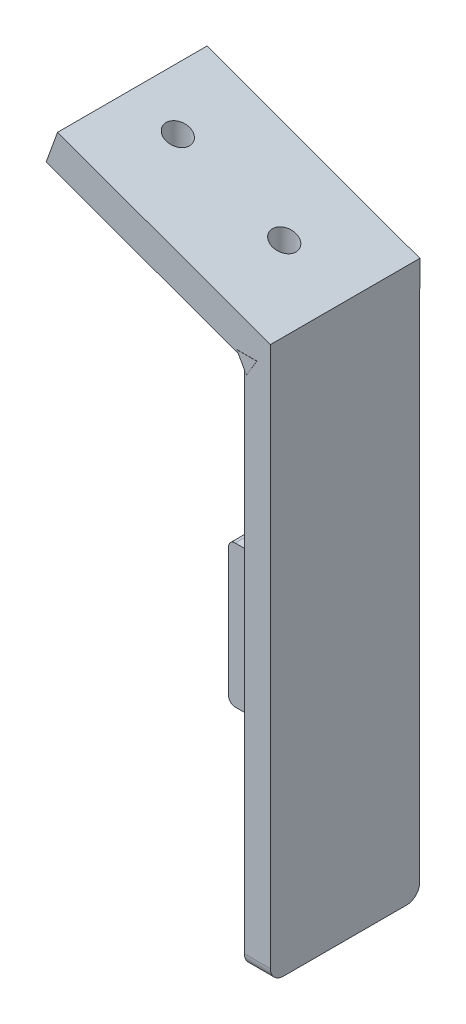
SolidWorks part; units mm, degrees
ref_plane "Plan de face" through (0, 0, 0) normal (0, 0, 1) x (1, 0, 0)
ref_plane "Plan de dessus" through (0, 0, 0) normal (0, 1, 0) x (1, 0, 0)
ref_plane "Plan de droite" through (0, 0, 0) normal (1, 0, 0) x (0, 0, -1)
sketch "Esquisse1" plane through (0, 0, 0) normal (0, 0, 1) x (1, 0, 0)
  line L0 (0, 26.549) -> (0, -58.451)
  line L1 (0, -58.451) -> (-4, -58.451)
  line L2 (-4, -58.451) -> (-4, 26.549)
  line L8 (-4, 26.549) -> (0, 26.549)
extrude "Boss.-Extru.1" add sketch "Esquisse1" along normal blind 22.93
sketch "Esquisse2" plane through (0, 0, 22.93) normal (0, 0, 1) x (1, 0, 0)
  line L4 (-32.6819, 38.4443) -> (0, 26.549)
  line L5 (-4, 26.549) -> (-4, -58.451) construction
  line L6 (0, 26.549) -> (0, 22.549)
  line L7 (0, -58.451) -> (0, 26.549) construction
  line L8 (0, 22.549) -> (-4, 22.549)
  line L9 (-4, 22.549) -> (-34.4354, 33.6266)
  line L10 (-34.4354, 33.6266) -> (-32.6819, 38.4443)
extrude "Boss.-Extru.5" add sketch "Esquisse2" against normal blind 22.95
sketch "Esquisse5" plane through (0, 0, 22.93) normal (0, 0, 1) x (1, 0, 0)
  line L1 (0, -58.451) -> (0, 26.549) construction
  line L2 (0, -21.471) -> (-25.35, -21.471)
  line L5 (-25.35, -21.471) -> (-25.35, -32.571)
  line L6 (-25.35, -32.571) -> (0, -32.571)
  line L7 (0, -32.571) -> (0, -21.471)
sketch "Esquisse7" plane through (0, 0, 0) normal (1, 0, 0) x (0, 0, -1)
  line L0 (0, -43.2913) -> (0, -21.471)
  line L1 (0, 22.549) -> (0, -58.451) construction
  line L2 (-22.93, -32.571) -> (-22.93, -21.471) construction
  line L4 (0, -21.471) -> (0, -43.2913) construction
  line L6 (0, -43.2913) -> (-4, -43.2913)
  line L7 (-4, -43.2913) -> (-4, -21.471)
  line L8 (-4, -21.471) -> (0, -21.471)
fillet "Congé1" radius 2 2 edges at (-2, -58.451, 0) (-2, -58.451, 22.93)
extrude "Boss.-Extru.10" add sketch "Esquisse7" against normal blind 25.35
fillet "Congé14" radius 1 2 edges at (-25.35, -43.2913, 2) (-25.35, -21.471, 2)
fillet "Congé15" radius 1 5 edges at (-25.0571, -42.9984, 0) (-25.35, -32.3812, 0) (-25.0571, -21.7639, 0) (-14.175, -43.2913, 0) (-14.175, -21.471, 0)
sketch "Esquisse9" plane through (0, 0, 0) normal (0, 1, 0) x (1, 0, 0)
  line L0 (-18.7784, -11.3774) -> (0, -11.455) construction
  line L1 (-18.7784, -11.3774) -> (-32.6819, -11.455) construction
  line L2 (-32.6819, 0.02) -> (-32.6819, -22.93) construction
  line L3 (0, -22.93) -> (0, 0.02) construction
  circle A0 centre (-25.7302, -11.4162) radius 1.8
  circle A1 centre (-9.3892, -11.4162) radius 1.8
extrude "Enlèv. mat.-Extru.1" cut sketch "Esquisse9" along normal blind 58
sketch "Esquisse10" plane through (-4, 0, 0) normal (-1, 0, 0) x (0, 0, 1)
  line L0 (7.7514, 10.4645) -> (12.7514, 10.4645)
  line L1 (12.7514, 10.4645) -> (12.7514, 15.4645)
  line L2 (12.7514, 15.4645) -> (10.7514, 15.4645)
  line L3 (10.7514, 15.4645) -> (10.7514, 12.4645)
  line L4 (10.7514, 12.4645) -> (7.7514, 12.4645)
  line L5 (7.7514, 12.4645) -> (7.7514, 10.4645)
extrude "Boss.-Extru.11" add sketch "Esquisse10" along normal blind 1
sketch "Esquisse12" plane through (0, 0, 0) normal (1, 0, 0) x (0, 0, -1)
  line L0 (0, -34.7689) -> (-4, -34.7689) construction
  line L1 (0, -56.451) -> (0, 22.549) construction
sketch "Esquisse13" plane through (0, 0, 0) normal (0, 0, 1) x (1, 0, 0)
  line L3 (-5.152, 23.3206) -> (-3.6562, 20.6811)
  line L4 (-3.6562, 20.6811) -> (-2.0751, 23.3206)
  line L5 (-2.0751, 23.3206) -> (-5.152, 23.3206)
extrude "Boss.-Extru.12" add sketch "Esquisse13" along normal blind 22.95
